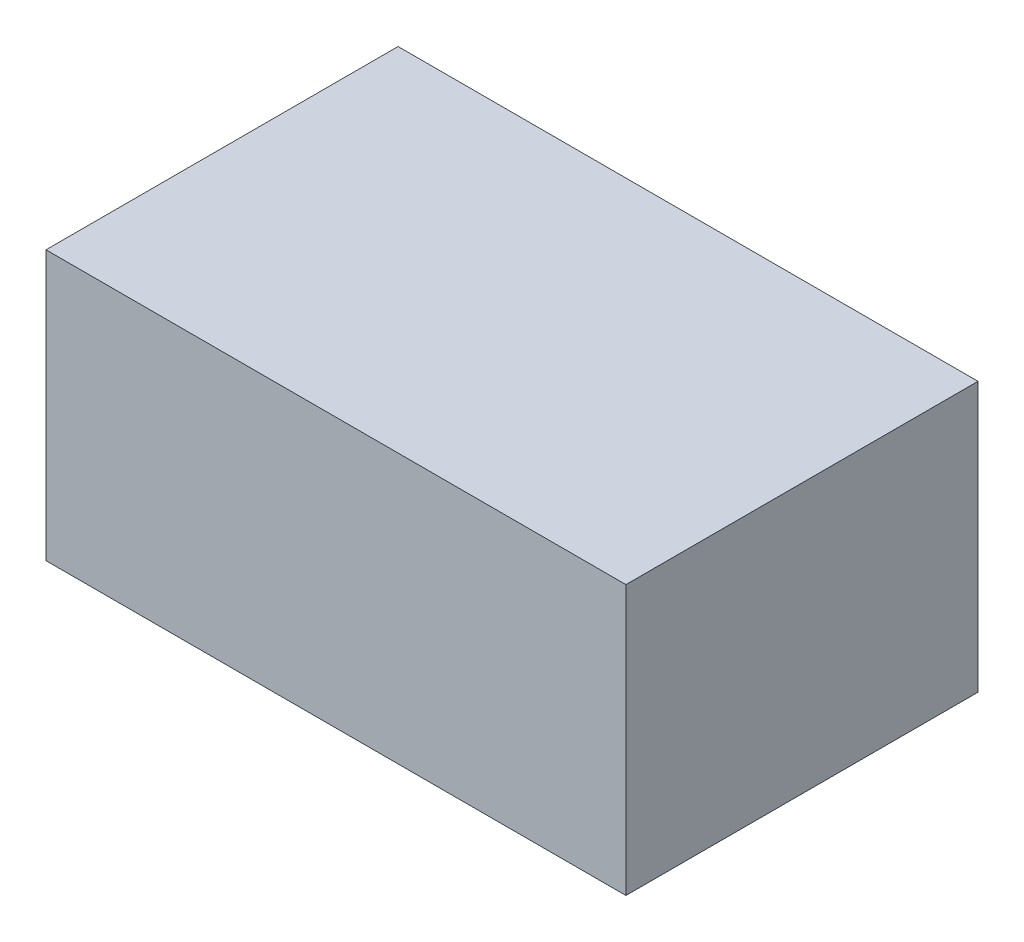
SolidWorks part; units mm, degrees
ref_plane "Front Plane" through (0, 0, 0) normal (0, 0, 1) x (1, 0, 0)
ref_plane "Top Plane" through (0, 0, 0) normal (0, 1, 0) x (1, 0, 0)
ref_plane "Right Plane" through (0, 0, 0) normal (1, 0, 0) x (0, 0, -1)
sketch "Sketch1" plane through (0, 0, 0) normal (0, 1, 0) x (1, 0, 0)
  line L1 (-35.56, 21.59) -> (35.56, 21.59)
  line L2 (-35.56, 21.59) -> (-35.56, -21.59)
  line L3 (-35.56, -21.59) -> (35.56, -21.59)
  line L4 (35.56, 21.59) -> (35.56, -21.59)
  line L5 (-35.56, 21.59) -> (35.56, -21.59) construction
  line L6 (-35.56, -21.59) -> (35.56, 21.59) construction
  point P0 (0, 0)
  dimension "D1" = 71.12
  dimension "D2" = 43.18
extrude "Boss-Extrude1" add sketch "Sketch1" along normal mid plane 33.02
